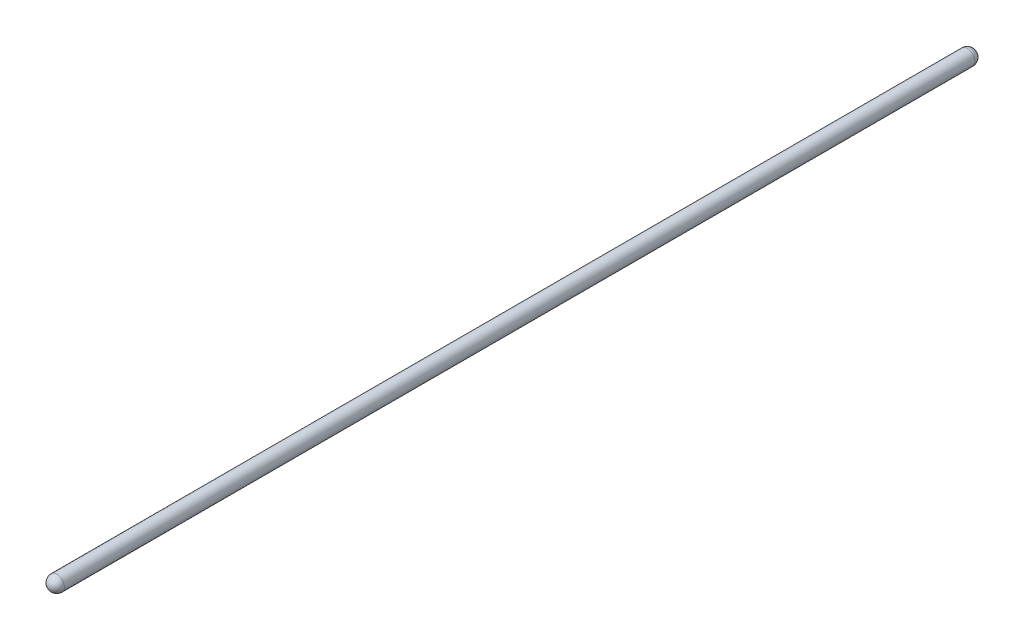
SolidWorks part; units mm, degrees
ref_plane "Front Plane" through (0, 0, 0) normal (0, 0, 1) x (1, 0, 0)
ref_plane "Top Plane" through (0, 0, 0) normal (0, 1, 0) x (1, 0, 0)
ref_plane "Right Plane" through (0, 0, 0) normal (1, 0, 0) x (0, 0, -1)
sketch "Sketch1" plane through (0, 0, 0) normal (0, 1, 0) x (1, 0, 0)
  line L0 (0, 0) -> (0, 9.525) construction
  line L1 (0, 0) -> (9.525, 0) construction
  line L2 (0, 0) -> (0, -1138.7633) construction
  line L3 (0, -1138.7633) -> (9.525, -1138.7633) construction
  line L4 (0, -1138.7633) -> (0, -1148.2883) construction
  line L5 (9.525, 0) -> (9.525, -1138.7633)
  line L6 (0, 9.525) -> (0, -1148.2883)
  arc A1 (0, 9.525) -> (9.525, 0) centre (0, 0) cw
  arc A2 (9.525, -1138.7633) -> (0, -1148.2883) centre (0, -1138.7633) cw
revolve "Revolve1" add sketch "Sketch1" angle 360 about L6
